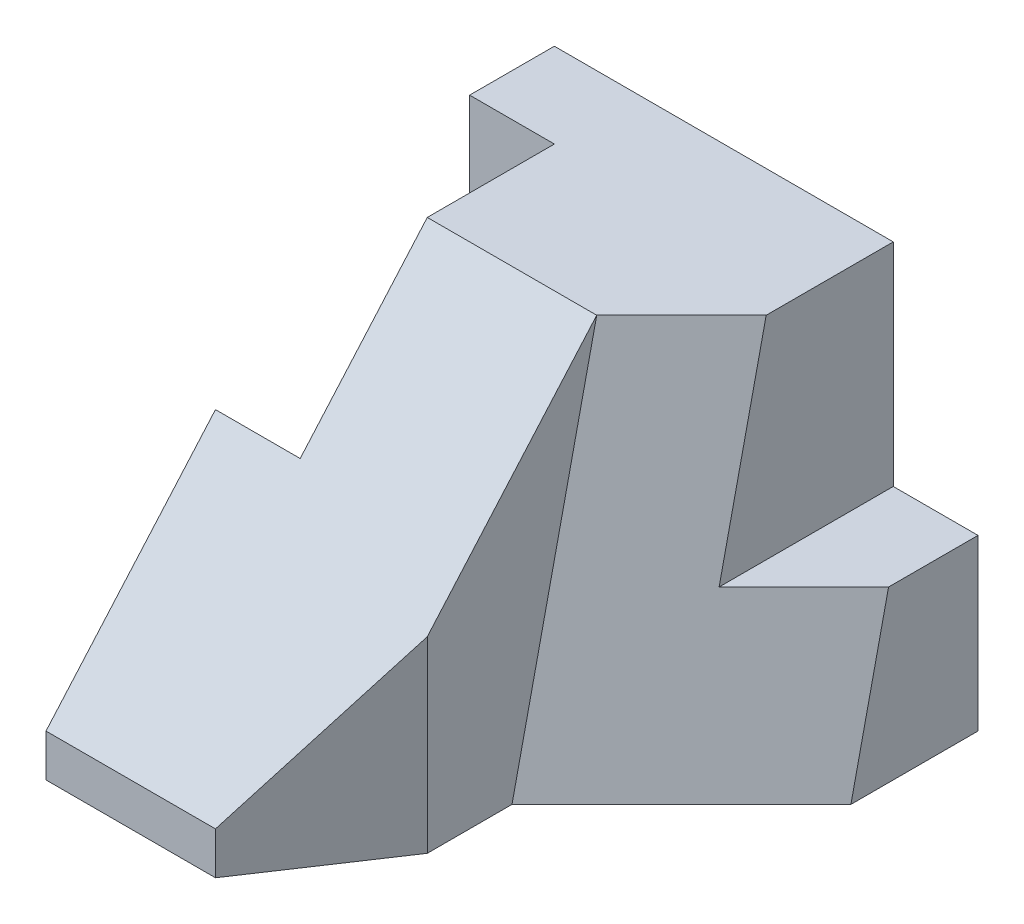
SolidWorks part; units mm, degrees
ref_plane "Front Plane" through (0, 0, 0) normal (0, 0, 1) x (1, 0, 0)
ref_plane "Top Plane" through (0, 0, 0) normal (0, 1, 0) x (1, 0, 0)
ref_plane "Right Plane" through (0, 0, 0) normal (1, 0, 0) x (0, 0, -1)
sketch "Sketch1" plane through (0, 0, 0) normal (0, 1, 0) x (1, 0, 0)
  line L1 (0, 0) -> (80, 0)
  line L2 (0, 0) -> (0, 50)
  line L3 (0, 50) -> (80, 50)
  line L4 (80, 0) -> (80, 50)
  dimension "D1" = 80
  dimension "D2" = 50
extrude "Boss-Extrude1" add sketch "Sketch1" along normal blind 90
sketch "Sketch2" plane through (0, 90, 0) normal (0, 1, 0) x (1, 0, 0)
  line L1 (0, 0) -> (20, 0)
  line L2 (0, 0) -> (0, 30)
  line L3 (0, 30) -> (20, 30)
  line L4 (20, 0) -> (20, 30)
  dimension "D1" = 20
  dimension "D2" = 30
extrude "Cut-Extrude1" cut sketch "Sketch2" against normal blind 90
sketch "Sketch3" plane through (80, 0, 0) normal (1, 0, 0) x (0, 0, -1)
  line L0 (50, 0) -> (20, 0)
  line L1 (0, 0) -> (50, 0) construction
  line L2 (20, 0) -> (50, 0)
  line L3 (50, 40) -> (30, 40)
  line L4 (50, 90) -> (50, 0) construction
  line L5 (30, 40) -> (20, 0)
  line M1 (0, 0) -> (50, 0)
  line M2 (50, 0) -> (50, 90)
  dimension "D1" = 20
  dimension "D2" = 40
  dimension "D3" = 30
extrude "Boss-Extrude2" add sketch "Sketch3" along normal blind 20 contours L3 L5 M1 M2
sketch "Sketch4" plane through (0, 90, 0) normal (0, 1, 0) x (1, 0, 0)
  line L0 (60, 0) -> (80, 20)
  line L1 (20, 0) -> (80, 0) construction
  line L2 (80, 0) -> (80, 50) construction
  line L3 (80, 20) -> (80, 0)
  line L4 (80, 0) -> (60, 0)
  dimension "D1" = 20
  dimension "D2" = 20
extrude "Cut-Extrude2" cut sketch "Sketch4" against normal blind 127
sketch "Sketch5" plane through (0, 0, 0) normal (0, -1, 0) x (-1, 0, 0)
  line L0 (-100, 20) -> (-60, -20)
  line L9 (-80, 20) -> (-100, 20)
  dimension "D1" = 40
  dimension "D2" = 40
ref_plane "Plane1" through (39.0361, 8.6747, 39.0361) normal (0.6985, 0.1552, 0.6985) x (0.7156, -0.1515, -0.6819)
ref_plane "Plane2" through (38.7879, 9.697, 38.7879) normal (0.6963, 0.1741, 0.6963) x (0.7177, -0.1689, -0.6755)
sketch "Sketch7" plane through (38.7879, 9.697, 38.7879) normal (0.6963, 0.1741, 0.6963) x (0.7177, -0.1689, -0.6755)
  line L0 (29.554, -4.8507) -> (85.2845, 4.8507)
  line L1 (85.2845, 4.8507) -> (85.2845, 46.0818)
  line L2 (85.2845, 46.0818) -> (29.554, -4.8507)
extrude "Boss-Extrude10" add sketch "Sketch7" against normal blind 38
ref_plane "Plane3" through (39.8608, 8.6185, 38.7834) normal (0.7083, 0.1531, 0.6891) x (0.6736, 0.1456, -0.7246)
ref_plane "Plane4" through (40.1565, 8.3082, 38.7718) normal (0.7116, 0.1472, 0.687) x (0.6728, 0.1392, -0.7266)
ref_plane "Plane5" through (39.0361, 8.6747, 39.0361) normal (0.6985, 0.1552, 0.6985) x (0.7156, -0.1515, -0.6819)
sketch "Sketch10" plane through (39.0361, 8.6747, 39.0361) normal (0.6985, 0.1552, 0.6985) x (0.7156, -0.1515, -0.6819)
  line L0 (57.246, 92.1954) -> (15.3217, 85.6875)
  line L1 (57.246, 92.1954) -> (29.2965, 87.8568) construction
  line L2 (15.3217, 85.6875) -> (29.2965, -4.3386)
  line L3 (29.2965, -4.3386) -> (85.1956, 4.3386)
  line L4 (85.1956, 4.3386) -> (85.1956, 46.2366)
  line L5 (85.1956, 46.2366) -> (57.246, 92.1954)
extrude "Boss-Extrude16" add sketch "Sketch10" against normal blind 38
sketch "Sketch11" plane through (100, 0, 0) normal (1, 0, 0) x (0, 0, -1)
  line L0 (20, 0) -> (29.0889, 40.9002)
  line L1 (29.0889, 40.9002) -> (30, 40)
  line L2 (30, 40) -> (20, 0)
extrude "Boss-Extrude17" add sketch "Sketch11" against normal blind 38
sketch "Sketch13" plane through (80, 0, 0) normal (1, 0, 0) x (0, 0, -1)
  line L1 (20, 90) -> (50, 90)
  line L2 (20, 90) -> (20, 40)
  line L3 (20, 40) -> (50, 40)
  line L4 (50, 90) -> (50, 40)
extrude "Cut-Extrude4" cut sketch "Sketch13" along normal blind 38
sketch "Sketch14" plane through (0, 0, -50) normal (0, 0, -1) x (-1, 0, 0)
  line L1 (0, 90) -> (-100, 90)
  line L2 (0, 90) -> (0, 0)
  line L3 (0, 0) -> (-100, 0)
  line L4 (-100, 90) -> (-100, 0)
extrude "Cut-Extrude5" cut sketch "Sketch14" along normal blind 38
sketch "Sketch15" plane through (0, 0, 0) normal (0, -1, 0) x (1, 0, 0)
  line L1 (0, -50) -> (106.7768, -50)
  line L2 (0, -50) -> (0, 28.5182)
  line L3 (0, 28.5182) -> (106.7768, 28.5182)
  line L4 (106.7768, -50) -> (106.7768, 28.5182)
  dimension "D1" = 78.5182
  dimension "D2" = 106.7768
extrude "Cut-Extrude6" cut sketch "Sketch15" along normal blind 38
sketch "Sketch16" plane through (0, 0, 0) normal (0, -1, 0) x (-1, 0, 0)
  line L0 (-60, -20) -> (-60, -40)
  line L1 (-60, -40) -> (-40, -70)
  line L2 (-40, -70) -> (0, -70)
  line L3 (0, -70) -> (0, -30)
  line L4 (0, -30) -> (-20, -30)
  line L5 (-20, -30) -> (-20, 0)
  line L6 (-20, 0) -> (-40, 0)
  line L7 (-40, 0) -> (-60, -20)
  dimension "D1" = 20
  dimension "D2" = 20
  dimension "D3" = 30
  dimension "D4" = 40
  dimension "D5" = 40
  dimension "D6" = 20
  dimension "D7" = 30
  dimension "D8" = 30
extrude "Boss-Extrude18" add sketch "Sketch16" against normal blind 10
ref_plane "Plane6" through (0, 39.0265, 44.6018) normal (0, -0.6585, -0.7526) x (-1, 0, 0)
sketch "Sketch17" plane through (0, 39.0265, 44.6018) normal (0, -0.6585, -0.7526) x (-1, 0, 0)
  line L0 (-20, 67.7319) -> (0, -38.5696)
  line L1 (0, -38.5696) -> (-40, -38.5696)
  line L2 (-40, -38.5696) -> (-60, 67.7319)
  line L3 (-60, 67.7319) -> (-20, 67.7319)
extrude "Cut-Extrude7" cut sketch "Sketch17" against normal blind 10
sketch "Sketch18" plane through (0, 39.0265, 44.6018) normal (0, -0.6585, -0.7526) x (-1, 0, 0)
  line L0 (-20, 67.7319) -> (-60, 67.7319)
  line L1 (-60, 67.7319) -> (-40, -38.5696)
  line L2 (-40, -38.5696) -> (0, -38.5696)
  line L3 (0, -38.5696) -> (-20, 67.7319)
extrude "Boss-Extrude19" add sketch "Sketch18" along normal blind 112
sketch "Sketch19" plane through (0, 0, -50) normal (0, 0, -1) x (-1, 0, 0)
  line L1 (0, 0) -> (-80, 0)
  line L2 (0, 0) -> (0, 90)
  line L3 (0, 90) -> (-80, 90)
  line L4 (-80, 0) -> (-80, 90)
extrude "Cut-Extrude8" cut sketch "Sketch19" along normal blind 112
sketch "Sketch20" plane through (0, 0, 0) normal (0, -1, 0) x (1, 0, 0)
  line L0 (40, 70) -> (0, 70) construction
  line L1 (0, 70) -> (107.6662, 70)
  line L2 (0, 70) -> (0, -106.0741)
  line L3 (0, -106.0741) -> (107.6662, -106.0741)
  line L4 (107.6662, 70) -> (107.6662, -106.0741)
  line L5 (100, -20) -> (100, -50) construction
  dimension "D1" = 176.0741
  dimension "D2" = 107.6662
  dimension "D3" = 7.6662
extrude "Cut-Extrude9" cut sketch "Sketch20" along normal blind 112
sketch "Sketch21" plane through (0, 0, 0) normal (0, -1, 0) x (-1, 0, 0)
  line L1 (0, 30) -> (-20, 30)
  line L2 (0, 30) -> (0, -30)
  line L3 (0, -30) -> (-20, -30)
  line L4 (-20, 30) -> (-20, -30)
  dimension "D1" = 60
  dimension "D2" = 20
extrude "Cut-Extrude10" cut sketch "Sketch21" against normal blind 112
sketch "Sketch23" plane through (60, 0, 0) normal (1, 0, 0) x (0, 0, -1)
  line L3 (-20, 10) -> (-40, 10)
ref_plane "Plane8" through (0, 39.0265, 44.6018) normal (0, -0.6585, -0.7526) x (-1, 0, 0)
sketch "Sketch27" plane through (60, 0, 0) normal (1, 0, 0) x (0, 0, -1)
  line L1 (-40, 0) -> (-17.4314, 0)
  line L2 (-40, 0) -> (-40, 9.8393)
  line L3 (-40, 9.8393) -> (-17.4314, 9.8393)
  line L4 (-17.4314, 0) -> (-17.4314, 9.8393)
  dimension "D1" = 22.5686
  dimension "D2" = 9.8393
extrude "Boss-Extrude22" add sketch "Sketch27" against normal blind 20
ref_plane "Plane9" through (0, 39.0265, 44.6018) normal (0, -0.6585, -0.7526) x (-1, 0, 0)
sketch "Sketch31" plane through (0, 39.0265, 44.6018) normal (0, -0.6585, -0.7526) x (-1, 0, 0)
  line L0 (0, -38.5696) -> (-11.4286, 22.1741)
  line L1 (-11.4286, 22.1741) -> (0, 22.1741)
  line L2 (0, 22.1741) -> (0, -38.5696)
extrude "Boss-Extrude24" add sketch "Sketch31" along normal blind 91
sketch "Sketch32" plane through (0, 0, 0) normal (0, -1, 0) x (-1, 0, 0)
  line L1 (-20, 30) -> (-3.5398, 30)
  line L2 (-20, 30) -> (-20, -30)
  line L3 (-20, -30) -> (-3.5398, -30)
  line L4 (-3.5398, 30) -> (-3.5398, -30)
extrude "Cut-Extrude13" cut sketch "Sketch32" against normal blind 101
sketch "Sketch33" plane through (7.0085, -0.9924, 0.8683) normal (0.9828, -0.1392, 0.1218) x (0.1206, -0.0171, -0.9926)
  line L0 (-0.6521, -49.4309) -> (39.6478, -2.5658)
  line L1 (39.6478, -2.5658) -> (34.8007, 1.6022)
  line L2 (34.8007, 1.6022) -> (-58.1356, 0)
  line L3 (-58.1356, 0) -> (-0.6521, -49.4309)
extrude "Cut-Extrude14" cut sketch "Sketch33" against normal blind 101
sketch "Sketch34" plane through (0, 0, 0) normal (0, -1, 0) x (-1, 0, 0)
  line L0 (0, 50) -> (0, -70)
  line L1 (0, -70) -> (-40, -70)
  line L2 (-40, -70) -> (-40, 50)
  line L3 (-100, 50) -> (0, 50) construction
  line L4 (-40, 50) -> (0, 50)
  line L6 (-20, -30) -> (0, -30)
  line L7 (-20, -30) -> (-20, 30)
  line L8 (-20, 30) -> (0, 30)
  line L9 (0, -30) -> (0, 30)
  line M1 (-11.4286, 33.6735) -> (0, 36.9388)
  line M2 (0, 36.9388) -> (0, 50)
  line M3 (0, 50) -> (-100, 50)
  line M8 (-40, -70) -> (0, -70)
  line M9 (0, -70) -> (0, -58.5714)
  line M10 (0, -58.5714) -> (-3.5398, -30)
  line M11 (-3.5398, -30) -> (-20, -30)
  line M12 (-20, -30) -> (-20, 30)
  line M13 (-20, 30) -> (-10.9735, 30)
  line M14 (-10.9735, 30) -> (-11.4286, 33.6735)
  dimension "D1" = 60
  dimension "D2" = 20
extrude "Boss-Extrude25" add sketch "Sketch34" against normal blind 5 contours L6 L0 M10 | L2 M8 M9 M10 M11 M12 M13 M14 M1 M2 M3 | L8 L6 L0 M13 M12 M11 | L8 L0 M14 M1
sketch "Sketch35" plane through (0, 0, 0) normal (0, -1, 0) x (-1, 0, 0)
  line L0 (0, 50) -> (0, -70) construction
  line L1 (0, 30) -> (-20, 30)
  line L2 (0, 30) -> (0, -30)
  line L3 (0, -30) -> (-20, -30)
  line L4 (-20, 30) -> (-20, -30)
  dimension "D1" = 60
  dimension "D2" = 20
  dimension "D3" = 20
extrude "Cut-Extrude15" cut sketch "Sketch35" against normal blind 152
sketch "Sketch39" plane through (60, 0, 40) normal (0.8321, 0, 0.5547) x (0.5547, 0, -0.8321)
  line L0 (0, 10) -> (0, 40)
  line L1 (0, 40) -> (-36.0555, 10)
  line L2 (-36.0555, 10) -> (0, 10)
  dimension "D1" = 30
extrude "Boss-Extrude27" add sketch "Sketch39" against normal blind 20
ref_plane "Plane10" through (0, 39.0265, 44.6018) normal (0, 0.6585, 0.7526) x (1, 0, 0)
sketch "Sketch42" plane through (60, 0, 0) normal (1, 0, 0) x (0, 0, -1)
  line L1 (-40, 0) -> (-15, 0)
  line L2 (-40, 0) -> (-40, 10)
  line L3 (-40, 10) -> (-15, 10)
  line L4 (-15, 0) -> (-15, 10)
  dimension "D1" = 10
  dimension "D2" = 25
extrude "Boss-Extrude29" add sketch "Sketch42" against normal blind 20
ref_plane "Plane11" through (60, 0, 0) normal (1, 0, 0) x (0, 0, -1)
sketch "Sketch43" plane through (60, 0, 0) normal (1, 0, 0) x (0, 0, -1)
  line L0 (-40, 10) -> (-17.7778, 10)
  line L1 (-17.7778, 10) -> (0, 90)
  line L2 (0, 90) -> (-40, 40)
  line L3 (-40, 40) -> (-40, 10)
extrude "Boss-Extrude30" add sketch "Sketch43" against normal blind 20
sketch "Sketch44" plane through (0, 39.0265, 44.6018) normal (0, 0.6585, 0.7526) x (1, 0, 0)
  line L0 (40, -38.5696) -> (60, 67.7319)
  line L1 (60, 67.7319) -> (60, 3.7629)
  line L2 (60, 3.7629) -> (40, -38.5696)
extrude "Boss-Extrude31" add sketch "Sketch44" against normal blind 20
sketch "Sketch46" plane through (0, 0, 0) normal (0, -1, 0) x (-1, 0, 0)
  line L1 (0, -70) -> (-60, -70)
  line L2 (0, -70) -> (0, -20)
  line L3 (0, -20) -> (-60, -20)
  line L4 (-60, -70) -> (-60, -20)
extrude "Cut-Extrude19" cut sketch "Sketch46" along normal blind 20
sketch "Sketch47" plane through (0, 0, -20) normal (0, 0, -1) x (-1, 0, 0)
  line L0 (-80, 90) -> (-80, 40)
  line L1 (-80, 40) -> (-91.1111, 40)
  line L2 (-91.1111, 40) -> (-80, 90)
extrude "Cut-Extrude20" cut sketch "Sketch47" against normal blind 20
sketch "Sketch48" plane through (60, 0, 40) normal (0.8321, 0, 0.5547) x (0.5547, 0, -0.8321)
  line L0 (0, 0) -> (0, 64.4462)
  line L1 (0, 64.4462) -> (-38.0362, 32.2231)
  line L2 (-38.0362, 32.2231) -> (-36.0555, 0)
  line L3 (-36.0555, 0) -> (0, 0)
  dimension "D1" = 32.2231
  dimension "D2" = 38.0362
  dimension "D3" = 32.2231
extrude "Cut-Extrude21" cut sketch "Sketch48" along normal blind 10
